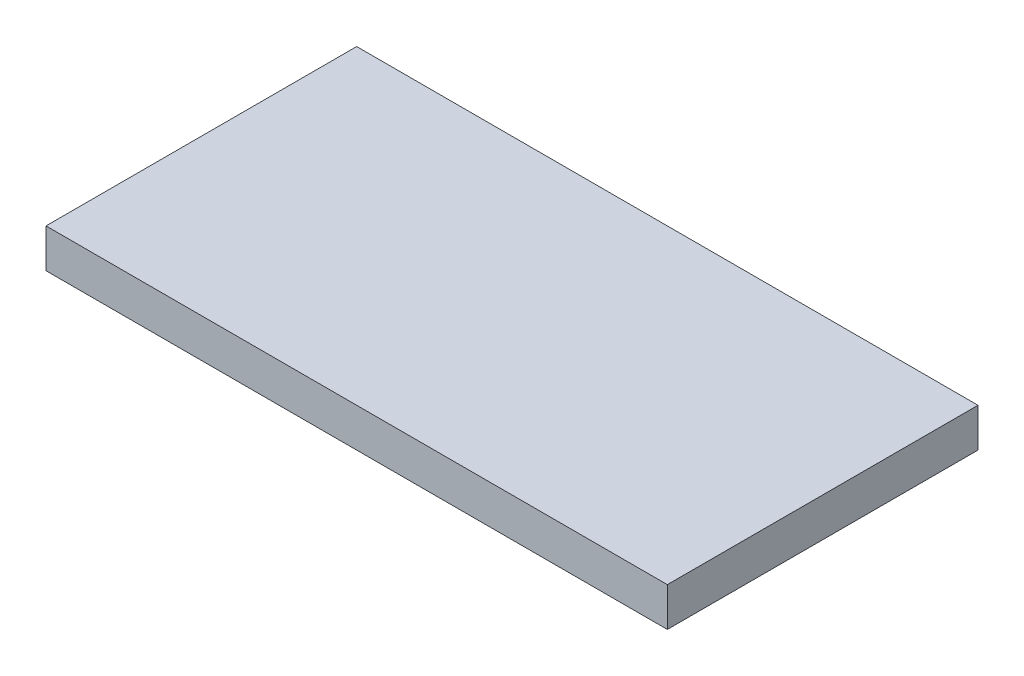
SolidWorks part; units mm, degrees
material "Polyurethane Foam Rigid"
ref_plane "Front Plane" through (0, 0, 0) normal (0, 0, 1) x (1, 0, 0)
ref_plane "Top Plane" through (0, 0, 0) normal (0, 1, 0) x (1, 0, 0)
ref_plane "Right Plane" through (0, 0, 0) normal (1, 0, 0) x (0, 0, -1)
sketch "Sketch1" plane through (0, 0, 0) normal (0, 1, 0) x (1, 0, 0)
  line L1 (-101.6, 50.8) -> (101.6, 50.8)
  line L2 (-101.6, 50.8) -> (-101.6, -50.8)
  line L3 (-101.6, -50.8) -> (101.6, -50.8)
  line L4 (101.6, 50.8) -> (101.6, -50.8)
  point P4 (0, 50.8)
  point P6 (-101.6, 0)
  dimension "D1" = 203.2
  dimension "D2" = 101.6
extrude "Boss-Extrude1" add sketch "Sketch1" along normal mid plane 12.7
